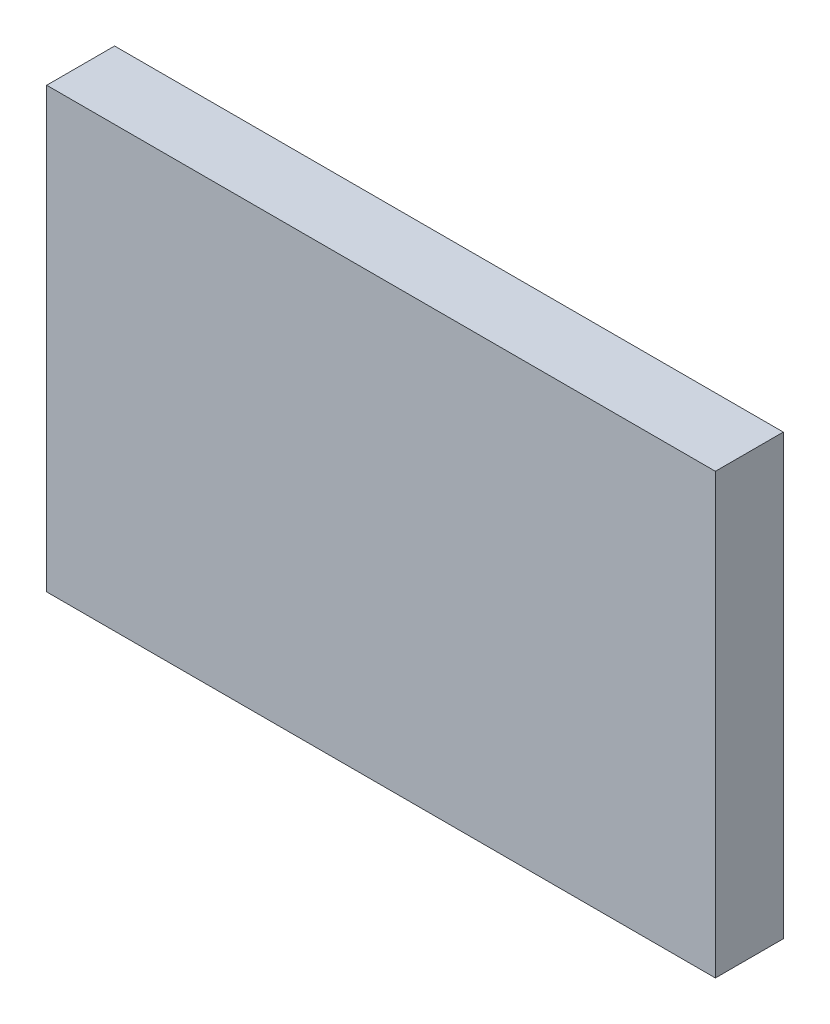
SolidWorks part; units mm, degrees
ref_plane "Plan de face" through (0, 0, 0) normal (0, 0, 1) x (1, 0, 0)
ref_plane "Plan de dessus" through (0, 0, 0) normal (0, 1, 0) x (1, 0, 0)
ref_plane "Plan de droite" through (0, 0, 0) normal (1, 0, 0) x (0, 0, -1)
sketch "Esquisse1" plane through (0, 0, 0) normal (0, 0, 1) x (1, 0, 0)
  line L1 (0, 0) -> (64, 0)
  line L2 (0, 0) -> (0, 42)
  line L3 (0, 42) -> (64, 42)
  line L4 (64, 0) -> (64, 42)
extrude "Boss.-Extru.1" add sketch "Esquisse1" along normal blind 6.5
